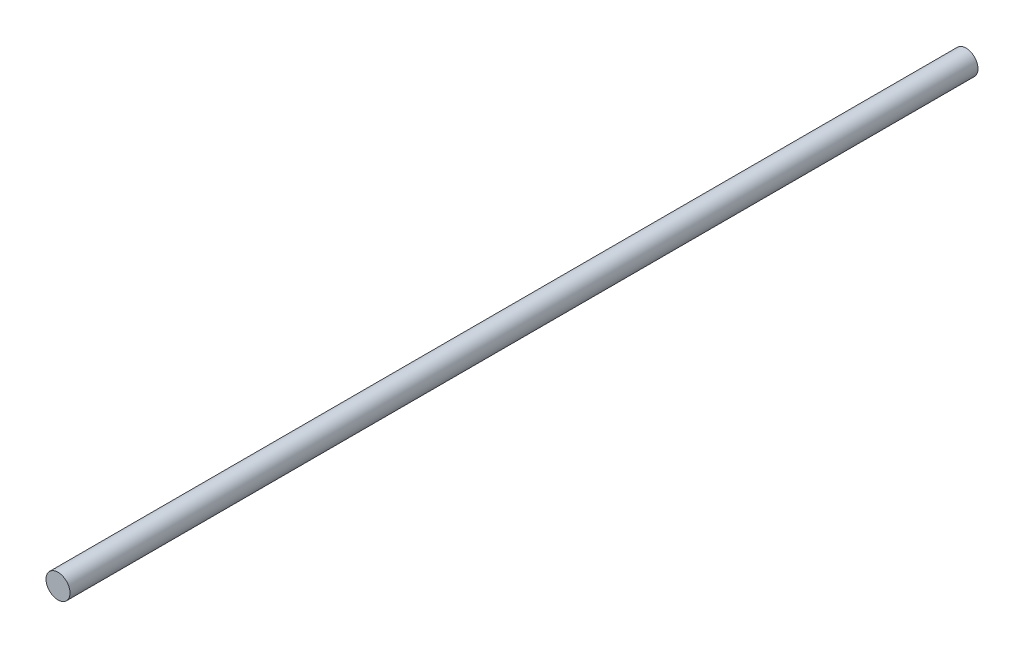
SolidWorks part; units mm, degrees
ref_plane "Front Plane" through (0, 0, 0) normal (0, 0, 1) x (1, 0, 0)
ref_plane "Top Plane" through (0, 0, 0) normal (0, 1, 0) x (1, 0, 0)
ref_plane "Right Plane" through (0, 0, 0) normal (1, 0, 0) x (0, 0, -1)
sketch "Sketch1" plane through (0, 0, 0) normal (0, 0, 1) x (1, 0, 0)
  circle A0 centre (0, 0) radius 2.3813
  dimension "D1" = 4.7625
extrude "Boss-Extrude1" add sketch "Sketch1" along normal mid plane 180
